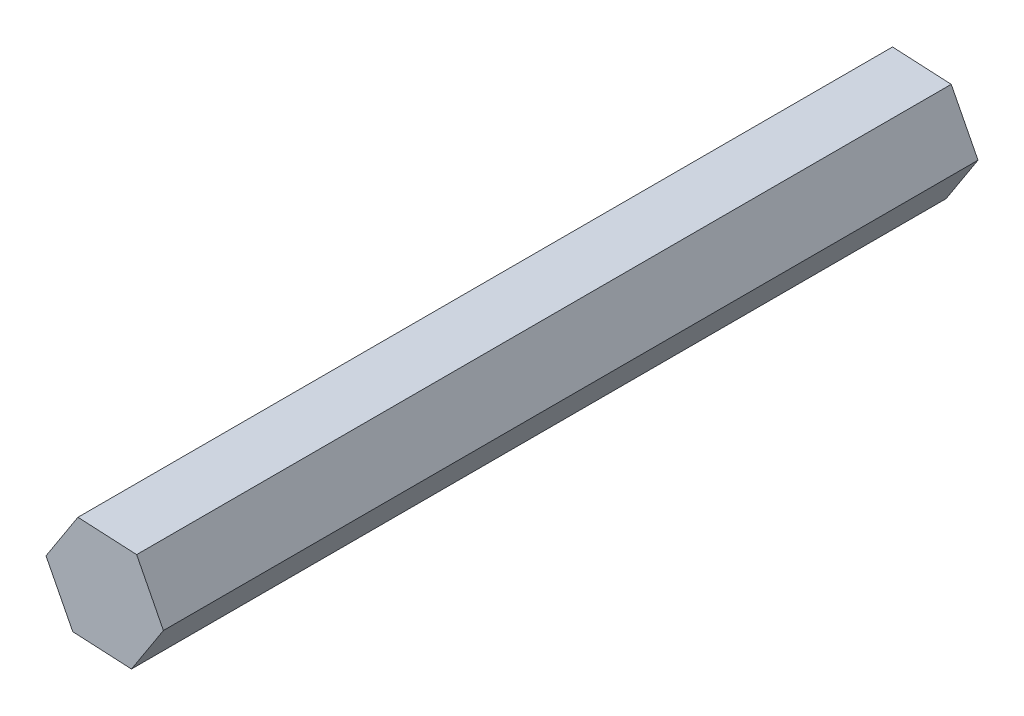
SolidWorks part; units mm, degrees
ref_plane "Front Plane" through (0, 0, 0) normal (0, 0, 1) x (1, 0, 0)
ref_plane "Top Plane" through (0, 0, 0) normal (0, 1, 0) x (1, 0, 0)
ref_plane "Right Plane" through (0, 0, 0) normal (1, 0, 0) x (0, 0, -1)
sketch "Sketch1" plane through (0, 0, 0) normal (0, 0, 1) x (1, 0, 0)
  line L1 (3.9845, 6.1552) -> (-3.3383, 6.5283)
  line L2 (-3.3383, 6.5283) -> (-7.3228, 0.3731)
  line L3 (-7.3228, 0.3731) -> (-3.9845, -6.1552)
  line L4 (-3.9845, -6.1552) -> (3.3383, -6.5283)
  line L5 (3.3383, -6.5283) -> (7.3228, -0.3731)
  line L6 (7.3228, -0.3731) -> (3.9845, 6.1552)
  circle A0 centre (0, 0) radius 6.35 construction
  dimension "D1" = 12.7
extrude "Boss-Extrude1" add sketch "Sketch1" along normal blind 101.6
